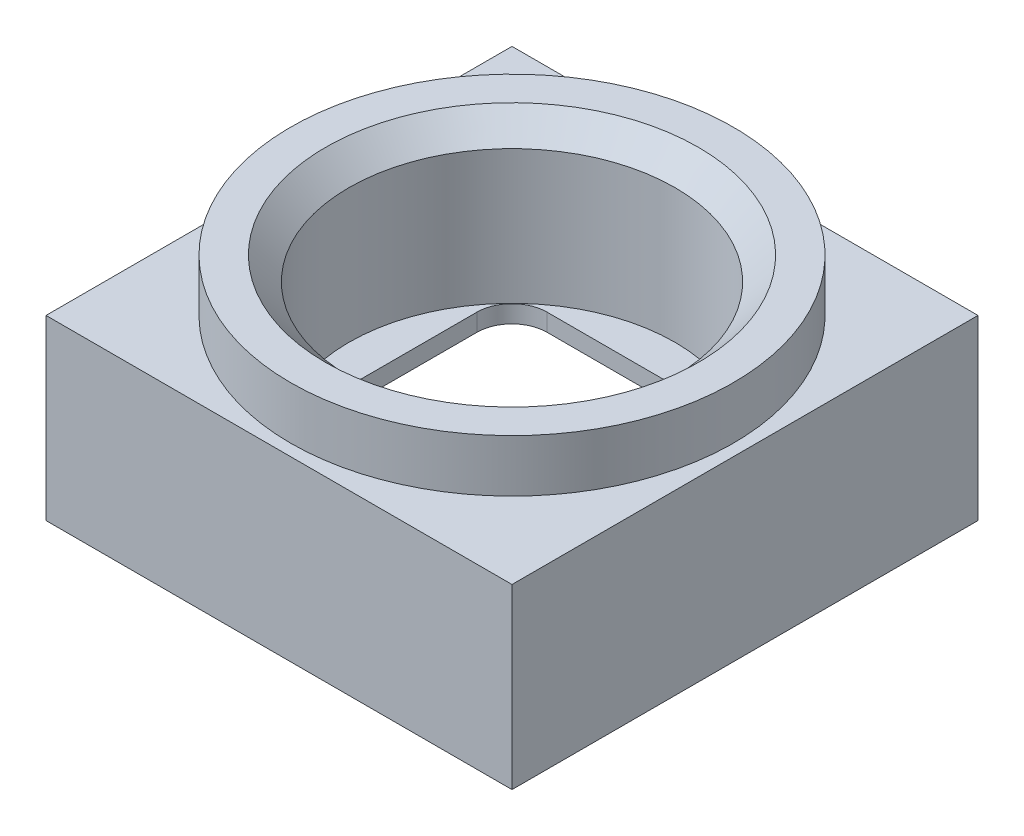
SolidWorks part; units mm, degrees
material "ABS PC"
ref_plane "Vorne" through (0, 0, 0) normal (0, 0, 1) x (1, 0, 0)
ref_plane "Oben" through (0, 0, 0) normal (0, 1, 0) x (1, 0, 0)
ref_plane "Rechts" through (0, 0, 0) normal (1, 0, 0) x (0, 0, -1)
sketch "downside" plane through (0, 0, 0) normal (0, 1, 0) x (1, 0, 0)
  line L0 (-4, 4) -> (4, -4) construction
  line L1 (-4, 4) -> (4, 4) construction
  line L2 (-4, 4) -> (-4, -4) construction
  line L3 (-4, -4) -> (4, -4) construction
  line L4 (4, 4) -> (4, -4) construction
  dimension "D1" = 8
sketch "side"
sketch "Skizze2" plane through (0, 0, 0) normal (0, 1, 0) x (1, 0, 0)
  line L0 (-4, 4) -> (4, 4) construction
  line L1 (-4, 4) -> (-4, -4) construction
  line L2 (4, 4) -> (4, -4) construction
  line L3 (-4, -4) -> (4, -4) construction
  line L4 (-4, 4) -> (4, 4)
  line L5 (-4, 4) -> (-4, -4)
  line L6 (4, 4) -> (4, -4)
  line L7 (-4, -4) -> (4, -4)
  line L8 (-3.7, 3.7) -> (3.7, 3.7)
  line L9 (3.7, 3.7) -> (3.7, -3.7)
  line L10 (-3.7, -3.7) -> (3.7, -3.7)
  line L11 (-3.7, 3.7) -> (-3.7, -3.7)
  dimension "D1" = 0.3
extrude "Aufsatz-Linear austragen1" add sketch "Skizze2" along normal blind 0.6
sketch "Skizze5" plane through (0, 0.6, 0) normal (0, 1, 0) x (1, 0, 0)
  line L0 (0, 0) -> (0, 3.2) construction
  line L1 (-2.7646, 3.2) -> (2.7646, 3.2)
  line L2 (-2.7646, -3.2) -> (2.7646, -3.2)
  line L3 (-3.2, 2.7646) -> (-3.2, -2.7646)
  line L4 (3.2, 2.7646) -> (3.2, -2.7646)
  line L5 (0, 0) -> (3.2, 0) construction
  line L11 (-4, 4) -> (-4, -4)
  line L12 (-4, -4) -> (4, -4)
  line L13 (4, -4) -> (4, 4)
  line L14 (4, 4) -> (-4, 4)
  line L15 (-4, 4) -> (-4, -4)
  line L16 (-4, -4) -> (4, -4)
  line L17 (4, -4) -> (4, 4)
  line L18 (4, 4) -> (-4, 4)
  arc A0 (3.2, 2.7646) -> (2.7646, 3.2) centre (3.1, 3.1) ccw
  arc A1 (3.2, -2.7646) -> (2.7646, -3.2) centre (3.1, -3.1) cw
  arc A2 (-3.2, -2.7646) -> (-2.7646, -3.2) centre (-3.1, -3.1) ccw
  arc A3 (-3.2, 2.7646) -> (-2.7646, 3.2) centre (-3.1, 3.1) cw
  point P17 (0, -3.2)
  dimension "D1" = 0.7
  dimension "D2" = 6.4
  dimension "D3" = 0.1
  dimension "D4" = 0
extrude "Aufsatz-Linear austragen3" add sketch "Skizze5" along normal blind 0.35
sketch "Skizze4" plane through (0, 0.95, 0) normal (0, 1, 0) x (1, 0, 0)
  line L0 (0, 2.15) -> (0, -2.15) construction
  line L1 (-1.55, 2.15) -> (1.55, 2.15)
  line L2 (-2.15, 1.55) -> (-2.15, -1.55)
  line L3 (-1.55, -2.15) -> (1.55, -2.15)
  line L4 (2.15, 1.55) -> (2.15, -1.55)
  line L9 (4, 4) -> (-4, 4)
  line L10 (-4, 4) -> (-4, -4)
  line L11 (-4, -4) -> (4, -4)
  line L12 (4, -4) -> (4, 4)
  line L13 (4, 4) -> (-4, 4)
  line L14 (-4, 4) -> (-4, -4)
  line L15 (-4, -4) -> (4, -4)
  line L16 (4, -4) -> (4, 4)
  arc A0 (-2.15, -1.55) -> (-1.55, -2.15) centre (-1.55, -1.55) ccw
  arc A1 (1.55, -2.15) -> (2.15, -1.55) centre (1.55, -1.55) ccw
  arc A2 (1.55, 2.15) -> (2.15, 1.55) centre (1.55, 1.55) cw
  arc A3 (-1.55, 2.15) -> (-2.15, 1.55) centre (-1.55, 1.55) ccw
  dimension "D1" = 0.6
  dimension "D2" = 4.3
  dimension "D3" = 0
extrude "Aufsatz-Linear austragen2" add sketch "Skizze4" along normal blind 0.3
sketch "Skizze7" plane through (0, 1.25, 0) normal (0, 1, 0) x (1, 0, 0)
  line L4 (4, -4) -> (4, 4)
  line L5 (4, 4) -> (-4, 4)
  line L6 (-4, 4) -> (-4, -4)
  line L7 (-4, -4) -> (4, -4)
  line L8 (4, -4) -> (4, 4)
  line L9 (4, 4) -> (-4, 4)
  line L10 (-4, 4) -> (-4, -4)
  line L11 (-4, -4) -> (4, -4)
  circle A0 centre (0, 0) radius 2.8
  dimension "D2" = 5.6
  dimension "D1" = 0
extrude "Aufsatz-Linear austragen4" add sketch "Skizze7" along normal blind 1.8
cosmetic thread "Gewindedarstellung1" parameters "D1"=2.1, "D2"=6
sketch "Skizze8" plane through (0, 3.05, 0) normal (0, 1, 0) x (1, 0, 0)
  circle A0 centre (0, 0) radius 3.8
  circle A1 centre (0, 0) radius 2.8 construction
  circle A2 centre (0, 0) radius 2.8
  dimension "D1" = 7.6
extrude "Aufsatz-Linear austragen5" add sketch "Skizze8" along normal blind 0.9
chamfer "Fase1" distance 0.4 angle 45 1 edges at (0, 3.95, 2.8)
